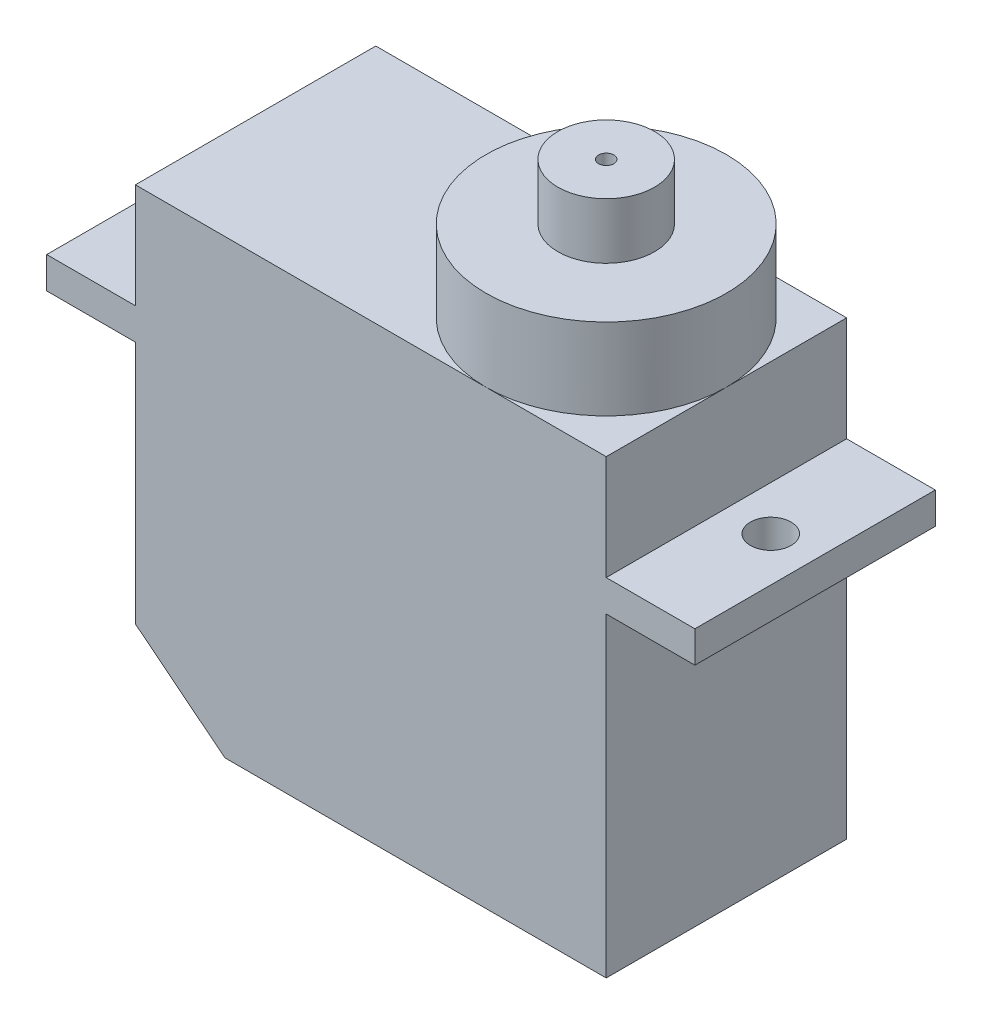
SolidWorks part; units mm, degrees
material "ABS"
ref_plane "Front Plane" through (0, 0, 0) normal (0, 0, 1) x (1, 0, 0)
ref_plane "Top Plane" through (0, 0, 0) normal (0, 1, 0) x (1, 0, 0)
ref_plane "Right Plane" through (0, 0, 0) normal (1, 0, 0) x (0, 0, -1)
sketch "Sketch1" plane through (0, 0, 0) normal (0, 1, 0) x (1, 0, 0)
  line L1 (0, 0) -> (23.15, 0)
  line L2 (0, 0) -> (0, 11.82)
  line L3 (0, 11.82) -> (23.15, 11.82)
  line L4 (23.15, 0) -> (23.15, 11.82)
  dimension "D1" = 11.82
  dimension "D2" = 23.15
extrude "Boss-Extrude1" add sketch "Sketch1" along normal blind 22.2
ref_plane "Plane1" through (0, 15.5, 0) normal (0, 1, 0) x (-1, 0, 0)
sketch "Sketch2" plane through (0, 15.5, 0) normal (0, 1, 0) x (-1, 0, 0)
  line L0 (0, 0) -> (-23.15, 0) construction
  line L1 (-27.51, -11.82) -> (4.36, -11.82)
  line L2 (-27.51, -11.82) -> (-27.51, 0)
  line L3 (-27.51, 0) -> (4.36, 0)
  line L4 (4.36, -11.82) -> (4.36, 0)
  line L5 (-23.15, -11.82) -> (0, -11.82) construction
  line L6 (-23.15, -5.91) -> (-27.51, -5.91) construction
  line L7 (-23.15, 0) -> (-23.15, -11.82) construction
  line L8 (0, -5.91) -> (4.36, -5.91) construction
  line L9 (0, -11.82) -> (0, 0) construction
  dimension "D1" = 31.87
extrude "Boss-Extrude2" add sketch "Sketch2" along normal blind 1.55
sketch "Sketch3" plane through (0, 15.5, 0) normal (0, 1, 0) x (-1, 0, 0)
  line L0 (-27.51, -5.91) -> (4.36, -5.91) construction
  line L1 (-27.51, 0) -> (-27.51, -11.82) construction
  line L2 (4.36, -11.82) -> (4.36, 0) construction
  line L4 (-25.33, 0) -> (-25.33, -11.82) construction
  line L5 (-23.15, 0) -> (-27.51, 0) construction
  line L6 (-27.51, -11.82) -> (-23.15, -11.82) construction
  line L7 (2.18, 0) -> (2.18, -11.82) construction
  line L8 (4.36, 0) -> (0, 0) construction
  line L9 (0, -11.82) -> (4.36, -11.82) construction
  circle A0 centre (-25.33, -5.91) radius 1
  circle A1 centre (2.18, -5.91) radius 1
  dimension "D1" = 2
  dimension "D2" = 27.51
extrude "Cut-Extrude1" cut sketch "Sketch3" along normal through all
sketch "Sketch4" plane through (0, 0, 0) normal (0, 0, 1) x (1, 0, 0)
  line L0 (-3.0756, 5.9465) -> (9.0263, -3.68)
  line L1 (9.0263, -3.68) -> (-2.5381, -3.68)
  line L2 (-2.5381, -3.68) -> (-3.0756, 5.9465)
  line L3 (0, 0) -> (23.15, 0) construction
  line L4 (-4.36, 15.5) -> (0, 15.5) construction
  point P2 (4.4, 0)
  point P4 (0, 3.5)
  dimension "D1" = 12
  dimension "D2" = 18.75
extrude "Cut-Extrude2" cut sketch "Sketch4" against normal through all
sketch "Sketch5" plane through (0, 22.2, 0) normal (0, 1, 0) x (1, 0, 0)
  line L0 (0, 5.91) -> (23.15, 5.91) construction
  line L1 (0, 11.82) -> (0, 0) construction
  line L2 (23.15, 0) -> (23.15, 11.82) construction
  line L3 (0, 0) -> (23.15, 0) construction
  circle A0 centre (17.24, 5.91) radius 5.91
extrude "Boss-Extrude3" add sketch "Sketch5" along normal blind 4
sketch "Sketch6" plane through (0, 26.2, 0) normal (0, 1, 0) x (1, 0, 0)
  circle A0 centre (17.24, 5.91) radius 2.375
  circle A1 centre (17.24, 5.91) radius 5.91 construction
  dimension "D1" = 4.75
extrude "Boss-Extrude4" add sketch "Sketch6" along normal blind 2.75
sketch "Sketch7" plane through (0, 28.95, 0) normal (0, 1, 0) x (1, 0, 0)
  circle A0 centre (17.24, 5.91) radius 0.375
  circle A1 centre (17.24, 5.91) radius 2.375 construction
  dimension "D1" = 0.75
extrude "Cut-Extrude3" cut sketch "Sketch7" against normal blind 2.75
